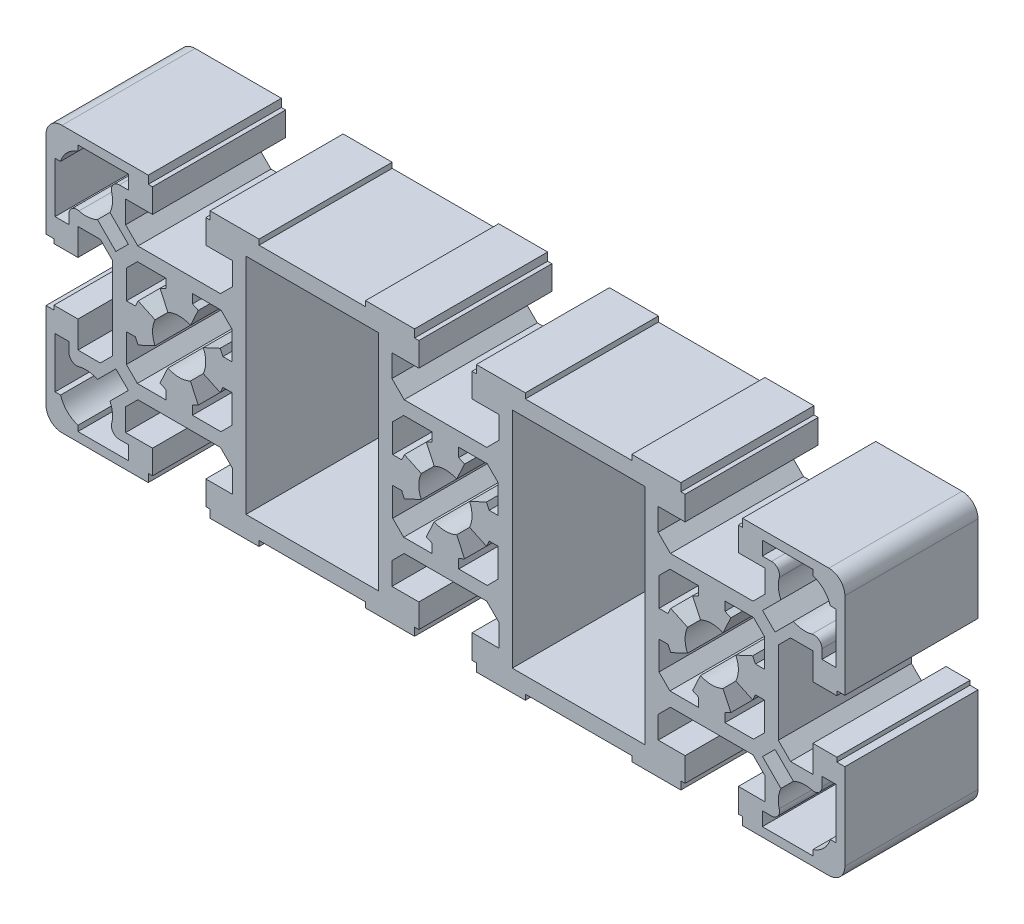
SolidWorks part; units mm, degrees
material "1060 Alloy"
ref_plane "Front" through (0, 0, 0) normal (0, 0, 1) x (1, 0, 0)
ref_plane "Top" through (0, 0, 0) normal (0, 1, 0) x (1, 0, 0)
ref_plane "Right" through (0, 0, 0) normal (1, 0, 0) x (0, 0, -1)
ref_plane "Plane1" through (0, 0, 0) normal (0, 0, 1) x (1, 0, 0)
sketch "Sketch1" plane through (0, 0, 0) normal (0, 0, 1) x (1, 0, 0)
  line L0 (72.2697, 19) -> (73.3, 19)
  line L1 (73.3, 19) -> (73.3, 9.5)
  line L2 (73.3, 9.5) -> (70.7, 9.5)
  line L3 (70.7, 9.5) -> (70.7, 11.2262)
  line L4 (65.3376, 12.9918) -> (61.8847, 9.5389)
  line L5 (61.8847, 9.5389) -> (59.5389, 11.8847)
  line L6 (59.5389, 11.8847) -> (62.9918, 15.3376)
  line L7 (61.2262, 20.7) -> (59.5, 20.7)
  line L8 (59.5, 20.7) -> (59.5, 23.3)
  line L9 (59.5, 23.3) -> (69, 23.3)
  line L10 (69, 23.3) -> (69, 22.2697)
  line L11 (62.9918, -15.3376) -> (59.5389, -11.8847)
  line L12 (59.5389, -11.8847) -> (61.8847, -9.5389)
  line L13 (61.8847, -9.5389) -> (65.3376, -12.9918)
  line L14 (70.7, -11.2262) -> (70.7, -9.5)
  line L15 (70.7, -9.5) -> (73.3, -9.5)
  line L16 (73.3, -9.5) -> (73.3, -19)
  line L17 (73.3, -19) -> (72.2697, -19)
  line L18 (69, -22.2697) -> (69, -23.3)
  line L19 (69, -23.3) -> (59.5, -23.3)
  line L20 (59.5, -23.3) -> (59.5, -20.7)
  line L21 (59.5, -20.7) -> (61.2262, -20.7)
  line L22 (-62.9918, 15.3376) -> (-59.5389, 11.8847)
  line L23 (-59.5389, 11.8847) -> (-61.8847, 9.5389)
  line L24 (-61.8847, 9.5389) -> (-65.3376, 12.9918)
  line L25 (-70.7, 11.2262) -> (-70.7, 9.5)
  line L26 (-70.7, 9.5) -> (-73.3, 9.5)
  line L27 (-73.3, 9.5) -> (-73.3, 19)
  line L28 (-73.3, 19) -> (-72.2697, 19)
  line L29 (-69, 22.2697) -> (-69, 23.3)
  line L30 (-69, 23.3) -> (-59.5, 23.3)
  line L31 (-59.5, 23.3) -> (-59.5, 20.7)
  line L32 (-59.5, 20.7) -> (-61.2262, 20.7)
  line L33 (-61.2262, -20.7) -> (-59.5, -20.7)
  line L34 (-59.5, -20.7) -> (-59.5, -23.3)
  line L35 (-59.5, -23.3) -> (-69, -23.3)
  line L36 (-69, -23.3) -> (-69, -22.2697)
  line L37 (-72.2697, -19) -> (-73.3, -19)
  line L38 (-73.3, -19) -> (-73.3, -9.5)
  line L39 (-73.3, -9.5) -> (-70.7, -9.5)
  line L40 (-70.7, -9.5) -> (-70.7, -11.2262)
  line L41 (-65.3376, -12.9918) -> (-61.8847, -9.5389)
  line L42 (-61.8847, -9.5389) -> (-59.5389, -11.8847)
  line L43 (-59.5389, -11.8847) -> (-62.9918, -15.3376)
  line L44 (-3.5923, 7.7036) -> (-2.1131, 4.5315)
  line L45 (2.1131, 4.5315) -> (3.5923, 7.7036)
  line L46 (3.5923, 7.7036) -> (2.5, 8.2129)
  line L47 (2.5, 8.2129) -> (2.5, 9.9)
  line L48 (2.5, 9.9) -> (7.8466, 9.9)
  line L49 (7.8466, 9.9) -> (9.9, 7.8466)
  line L50 (9.9, 7.8466) -> (9.9, 2.5)
  line L51 (9.9, 2.5) -> (8.2129, 2.5)
  line L52 (8.2129, 2.5) -> (7.7036, 3.5923)
  line L53 (7.7036, 3.5923) -> (4.5315, 2.1131)
  line L54 (4.5315, -2.1131) -> (7.7036, -3.5923)
  line L55 (7.7036, -3.5923) -> (8.2129, -2.5)
  line L56 (8.2129, -2.5) -> (9.9, -2.5)
  line L57 (9.9, -2.5) -> (9.9, -7.8466)
  line L58 (9.9, -7.8466) -> (7.8466, -9.9)
  line L59 (7.8466, -9.9) -> (2.5, -9.9)
  line L60 (2.5, -9.9) -> (2.5, -8.2129)
  line L61 (2.5, -8.2129) -> (3.5923, -7.7036)
  line L62 (3.5923, -7.7036) -> (2.1131, -4.5315)
  line L63 (-2.1131, -4.5315) -> (-3.5923, -7.7036)
  line L64 (-3.5923, -7.7036) -> (-2.5, -8.2129)
  line L65 (-2.5, -8.2129) -> (-2.5, -9.9)
  line L66 (-2.5, -9.9) -> (-7.8466, -9.9)
  line L67 (-7.8466, -9.9) -> (-9.9, -7.8466)
  line L68 (-9.9, -7.8466) -> (-9.9, -2.5)
  line L69 (-9.9, -2.5) -> (-8.2129, -2.5)
  line L70 (-8.2129, -2.5) -> (-7.7036, -3.5923)
  line L71 (-7.7036, -3.5923) -> (-4.5315, -2.1131)
  line L72 (-4.5315, 2.1131) -> (-7.7036, 3.5923)
  line L73 (-7.7036, 3.5923) -> (-8.2129, 2.5)
  line L74 (-8.2129, 2.5) -> (-9.9, 2.5)
  line L75 (-9.9, 2.5) -> (-9.9, 7.8466)
  line L76 (-9.9, 7.8466) -> (-7.8466, 9.9)
  line L77 (-7.8466, 9.9) -> (-2.5, 9.9)
  line L78 (-2.5, 9.9) -> (-2.5, 8.2129)
  line L79 (-2.5, 8.2129) -> (-3.5923, 7.7036)
  line L80 (52.5, 8.2129) -> (52.5, 9.9)
  line L81 (52.5, 9.9) -> (57.8466, 9.9)
  line L82 (57.8466, 9.9) -> (59.9, 7.8466)
  line L83 (59.9, 7.8466) -> (59.9, 2.5)
  line L84 (59.9, 2.5) -> (58.2129, 2.5)
  line L85 (58.2129, 2.5) -> (57.7036, 3.5923)
  line L86 (57.7036, 3.5923) -> (54.5315, 2.1131)
  line L87 (54.5315, -2.1131) -> (57.7036, -3.5923)
  line L88 (57.7036, -3.5923) -> (58.2129, -2.5)
  line L89 (58.2129, -2.5) -> (59.9, -2.5)
  line L90 (59.9, -2.5) -> (59.9, -7.8466)
  line L91 (59.9, -7.8466) -> (57.8466, -9.9)
  line L92 (57.8466, -9.9) -> (52.5, -9.9)
  line L93 (52.5, -9.9) -> (52.5, -8.2129)
  line L94 (52.5, -8.2129) -> (53.5923, -7.7036)
  line L95 (53.5923, -7.7036) -> (52.1131, -4.5315)
  line L96 (47.8869, -4.5315) -> (46.4077, -7.7036)
  line L97 (46.4077, -7.7036) -> (47.5, -8.2129)
  line L98 (47.5, -8.2129) -> (47.5, -9.9)
  line L99 (47.5, -9.9) -> (42.1534, -9.9)
  line L100 (42.1534, -9.9) -> (40.1, -7.8466)
  line L101 (40.1, -7.8466) -> (40.1, -2.5)
  line L102 (40.1, -2.5) -> (41.7871, -2.5)
  line L103 (41.7871, -2.5) -> (42.2964, -3.5923)
  line L104 (42.2964, -3.5923) -> (45.4685, -2.1131)
  line L105 (45.4685, 2.1131) -> (42.2964, 3.5923)
  line L106 (42.2964, 3.5923) -> (41.7871, 2.5)
  line L107 (41.7871, 2.5) -> (40.1, 2.5)
  line L108 (40.1, 2.5) -> (40.1, 7.8466)
  line L109 (40.1, 7.8466) -> (42.1534, 9.9)
  line L110 (42.1534, 9.9) -> (47.5, 9.9)
  line L111 (47.5, 9.9) -> (47.5, 8.2129)
  line L112 (47.5, 8.2129) -> (46.4077, 7.7036)
  line L113 (46.4077, 7.7036) -> (47.8869, 4.5315)
  line L114 (52.1131, 4.5315) -> (53.5923, 7.7036)
  line L115 (53.5923, 7.7036) -> (52.5, 8.2129)
  line L116 (-40.1, 2.5) -> (-41.7871, 2.5)
  line L117 (-41.7871, 2.5) -> (-42.2964, 3.5923)
  line L118 (-42.2964, 3.5923) -> (-45.4685, 2.1131)
  line L119 (-45.4685, -2.1131) -> (-42.2964, -3.5923)
  line L120 (-42.2964, -3.5923) -> (-41.7871, -2.5)
  line L121 (-41.7871, -2.5) -> (-40.1, -2.5)
  line L122 (-40.1, -2.5) -> (-40.1, -7.8466)
  line L123 (-40.1, -7.8466) -> (-42.1534, -9.9)
  line L124 (-42.1534, -9.9) -> (-47.5, -9.9)
  line L125 (-47.5, -9.9) -> (-47.5, -8.2129)
  line L126 (-47.5, -8.2129) -> (-46.4077, -7.7036)
  line L127 (-46.4077, -7.7036) -> (-47.8869, -4.5315)
  line L128 (-52.1131, -4.5315) -> (-53.5923, -7.7036)
  line L129 (-53.5923, -7.7036) -> (-52.5, -8.2129)
  line L130 (-52.5, -8.2129) -> (-52.5, -9.9)
  line L131 (-52.5, -9.9) -> (-57.8466, -9.9)
  line L132 (-57.8466, -9.9) -> (-59.9, -7.8466)
  line L133 (-59.9, -7.8466) -> (-59.9, -2.5)
  line L134 (-59.9, -2.5) -> (-58.2129, -2.5)
  line L135 (-58.2129, -2.5) -> (-57.7036, -3.5923)
  line L136 (-57.7036, -3.5923) -> (-54.5315, -2.1131)
  line L137 (-54.5315, 2.1131) -> (-57.7036, 3.5923)
  line L138 (-57.7036, 3.5923) -> (-58.2129, 2.5)
  line L139 (-58.2129, 2.5) -> (-59.9, 2.5)
  line L140 (-59.9, 2.5) -> (-59.9, 7.8466)
  line L141 (-59.9, 7.8466) -> (-57.8466, 9.9)
  line L142 (-57.8466, 9.9) -> (-52.5, 9.9)
  line L143 (-52.5, 9.9) -> (-52.5, 8.2129)
  line L144 (-52.5, 8.2129) -> (-53.5923, 7.7036)
  line L145 (-53.5923, 7.7036) -> (-52.1131, 4.5315)
  line L146 (-47.8869, 4.5315) -> (-46.4077, 7.7036)
  line L147 (-46.4077, 7.7036) -> (-47.5, 8.2129)
  line L148 (-47.5, 8.2129) -> (-47.5, 9.9)
  line L149 (-47.5, 9.9) -> (-42.1534, 9.9)
  line L150 (-42.1534, 9.9) -> (-40.1, 7.8466)
  line L151 (-40.1, 7.8466) -> (-40.1, 2.5)
  line L152 (-37.45, -21) -> (-37.45, 21)
  line L153 (-37.45, 21) -> (-12.55, 21)
  line L154 (-12.55, 21) -> (-12.55, -21)
  line L155 (-12.55, -21) -> (-37.45, -21)
  line L156 (12.55, 21) -> (37.45, 21)
  line L157 (37.45, 21) -> (37.45, -21)
  line L158 (37.45, -21) -> (12.55, -21)
  line L159 (12.55, -21) -> (12.55, 21)
  line L160 (73.5, 5) -> (73.5, 5.8)
  line L161 (73.5, 5.8) -> (75, 5.8)
  line L162 (75, 5.8) -> (75, 22)
  line L163 (72, 25) -> (55.8, 25)
  line L164 (55.8, 25) -> (55.8, 23.5)
  line L165 (55.8, 23.5) -> (55, 23.5)
  line L166 (55, 23.5) -> (55, 19)
  line L167 (55, 19) -> (60.05, 19)
  line L168 (60.05, 19) -> (60.05, 14.8)
  line L169 (60.05, 14.8) -> (57.75, 12.5)
  line L170 (57.75, 12.5) -> (42.25, 12.5)
  line L171 (42.25, 12.5) -> (39.95, 14.8)
  line L172 (39.95, 14.8) -> (39.95, 19)
  line L173 (39.95, 19) -> (45, 19)
  line L174 (45, 19) -> (45, 23.5)
  line L175 (45, 23.5) -> (44.2, 23.5)
  line L176 (44.2, 23.5) -> (44.2, 25)
  line L177 (44.2, 25) -> (35, 25)
  line L178 (35, 25) -> (35, 24)
  line L179 (35, 24) -> (15, 24)
  line L180 (15, 24) -> (15, 25)
  line L181 (15, 25) -> (5.8, 25)
  line L182 (5.8, 25) -> (5.8, 23.5)
  line L183 (5.8, 23.5) -> (5, 23.5)
  line L184 (5, 23.5) -> (5, 19)
  line L185 (5, 19) -> (10.05, 19)
  line L186 (10.05, 19) -> (10.05, 14.8)
  line L187 (10.05, 14.8) -> (7.75, 12.5)
  line L188 (7.75, 12.5) -> (-7.75, 12.5)
  line L189 (-7.75, 12.5) -> (-10.05, 14.8)
  line L190 (-10.05, 14.8) -> (-10.05, 19)
  line L191 (-10.05, 19) -> (-5, 19)
  line L192 (-5, 19) -> (-5, 23.5)
  line L193 (-5, 23.5) -> (-5.8, 23.5)
  line L194 (-5.8, 23.5) -> (-5.8, 25)
  line L195 (-5.8, 25) -> (-15, 25)
  line L196 (-15, 25) -> (-15, 24)
  line L197 (-15, 24) -> (-35, 24)
  line L198 (-35, 24) -> (-35, 25)
  line L199 (-35, 25) -> (-44.2, 25)
  line L200 (-44.2, 25) -> (-44.2, 23.5)
  line L201 (-44.2, 23.5) -> (-45, 23.5)
  line L202 (-45, 23.5) -> (-45, 19)
  line L203 (-45, 19) -> (-39.95, 19)
  line L204 (-39.95, 19) -> (-39.95, 14.8)
  line L205 (-39.95, 14.8) -> (-42.25, 12.5)
  line L206 (-42.25, 12.5) -> (-57.75, 12.5)
  line L207 (-57.75, 12.5) -> (-60.05, 14.8)
  line L208 (-60.05, 14.8) -> (-60.05, 19)
  line L209 (-60.05, 19) -> (-55, 19)
  line L210 (-55, 19) -> (-55, 23.5)
  line L211 (-55, 23.5) -> (-55.8, 23.5)
  line L212 (-55.8, 23.5) -> (-55.8, 25)
  line L213 (-55.8, 25) -> (-72, 25)
  line L214 (-75, 22) -> (-75, 5.8)
  line L215 (-75, 5.8) -> (-73.5, 5.8)
  line L216 (-73.5, 5.8) -> (-73.5, 5)
  line L217 (-73.5, 5) -> (-69, 5)
  line L218 (-69, 5) -> (-69, 10.05)
  line L219 (-69, 10.05) -> (-64.8, 10.05)
  line L220 (-64.8, 10.05) -> (-62.5, 7.75)
  line L221 (-62.5, 7.75) -> (-62.5, -7.75)
  line L222 (-62.5, -7.75) -> (-64.8, -10.05)
  line L223 (-64.8, -10.05) -> (-69, -10.05)
  line L224 (-69, -10.05) -> (-69, -5)
  line L225 (-69, -5) -> (-73.5, -5)
  line L226 (-73.5, -5) -> (-73.5, -5.8)
  line L227 (-73.5, -5.8) -> (-75, -5.8)
  line L228 (-75, -5.8) -> (-75, -22)
  line L229 (-72, -25) -> (-55.8, -25)
  line L230 (-55.8, -25) -> (-55.8, -23.5)
  line L231 (-55.8, -23.5) -> (-55, -23.5)
  line L232 (-55, -23.5) -> (-55, -19)
  line L233 (-55, -19) -> (-60.05, -19)
  line L234 (-60.05, -19) -> (-60.05, -14.8)
  line L235 (-60.05, -14.8) -> (-57.75, -12.5)
  line L236 (-57.75, -12.5) -> (-42.25, -12.5)
  line L237 (-42.25, -12.5) -> (-39.95, -14.8)
  line L238 (-39.95, -14.8) -> (-39.95, -19)
  line L239 (-39.95, -19) -> (-45, -19)
  line L240 (-45, -19) -> (-45, -23.5)
  line L241 (-45, -23.5) -> (-44.2, -23.5)
  line L242 (-44.2, -23.5) -> (-44.2, -25)
  line L243 (-44.2, -25) -> (-35, -25)
  line L244 (-35, -25) -> (-35, -24)
  line L245 (-35, -24) -> (-15, -24)
  line L246 (-15, -24) -> (-15, -25)
  line L247 (-15, -25) -> (-5.8, -25)
  line L248 (-5.8, -25) -> (-5.8, -23.5)
  line L249 (-5.8, -23.5) -> (-5, -23.5)
  line L250 (-5, -23.5) -> (-5, -19)
  line L251 (-5, -19) -> (-10.05, -19)
  line L252 (-10.05, -19) -> (-10.05, -14.8)
  line L253 (-10.05, -14.8) -> (-7.75, -12.5)
  line L254 (-7.75, -12.5) -> (7.75, -12.5)
  line L255 (7.75, -12.5) -> (10.05, -14.8)
  line L256 (10.05, -14.8) -> (10.05, -19)
  line L257 (10.05, -19) -> (5, -19)
  line L258 (5, -19) -> (5, -23.5)
  line L259 (5, -23.5) -> (5.8, -23.5)
  line L260 (5.8, -23.5) -> (5.8, -25)
  line L261 (5.8, -25) -> (15, -25)
  line L262 (15, -25) -> (15, -24)
  line L263 (15, -24) -> (35, -24)
  line L264 (35, -24) -> (35, -25)
  line L265 (35, -25) -> (44.2, -25)
  line L266 (44.2, -25) -> (44.2, -23.5)
  line L267 (44.2, -23.5) -> (45, -23.5)
  line L268 (45, -23.5) -> (45, -19)
  line L269 (45, -19) -> (39.95, -19)
  line L270 (39.95, -19) -> (39.95, -14.8)
  line L271 (39.95, -14.8) -> (42.25, -12.5)
  line L272 (42.25, -12.5) -> (57.75, -12.5)
  line L273 (57.75, -12.5) -> (60.05, -14.8)
  line L274 (60.05, -14.8) -> (60.05, -19)
  line L275 (60.05, -19) -> (55, -19)
  line L276 (55, -19) -> (55, -23.5)
  line L277 (55, -23.5) -> (55.8, -23.5)
  line L278 (55.8, -23.5) -> (55.8, -25)
  line L279 (55.8, -25) -> (72, -25)
  line L280 (75, -22) -> (75, -5.8)
  line L281 (75, -5.8) -> (73.5, -5.8)
  line L282 (73.5, -5.8) -> (73.5, -5)
  line L283 (73.5, -5) -> (69, -5)
  line L284 (69, -5) -> (69, -10.05)
  line L285 (69, -10.05) -> (64.8, -10.05)
  line L286 (64.8, -10.05) -> (62.5, -7.75)
  line L287 (62.5, -7.75) -> (62.5, 7.75)
  line L288 (62.5, 7.75) -> (64.8, 10.05)
  line L289 (64.8, 10.05) -> (69, 10.05)
  line L290 (69, 10.05) -> (69, 5)
  line L291 (69, 5) -> (73.5, 5)
  arc A0 (69, 22.2697) -> (72.2697, 19) centre (67.5, 17.5) cw
  arc A1 (70.7, 11.2262) -> (68.8077, 12.674) centre (69.2, 11.2262) ccw
  arc A2 (68.8077, 12.674) -> (65.3376, 12.9918) centre (67.5, 17.5) cw
  arc A3 (62.9918, 15.3376) -> (62.674, 18.8077) centre (67.5, 17.5) cw
  arc A4 (62.674, 18.8077) -> (61.2262, 20.7) centre (61.2262, 19.2) ccw
  arc A5 (65.3376, -12.9918) -> (68.8077, -12.674) centre (67.5, -17.5) cw
  arc A6 (68.8077, -12.674) -> (70.7, -11.2262) centre (69.2, -11.2262) ccw
  arc A7 (72.2697, -19) -> (69, -22.2697) centre (67.5, -17.5) cw
  arc A8 (61.2262, -20.7) -> (62.674, -18.8077) centre (61.2262, -19.2) ccw
  arc A9 (62.674, -18.8077) -> (62.9918, -15.3376) centre (67.5, -17.5) cw
  arc A10 (-61.2262, 20.7) -> (-62.674, 18.8077) centre (-61.2262, 19.2) ccw
  arc A11 (-62.674, 18.8077) -> (-62.9918, 15.3376) centre (-67.5, 17.5) cw
  arc A12 (-65.3376, 12.9918) -> (-68.8077, 12.674) centre (-67.5, 17.5) cw
  arc A13 (-68.8077, 12.674) -> (-70.7, 11.2262) centre (-69.2, 11.2262) ccw
  arc A14 (-72.2697, 19) -> (-69, 22.2697) centre (-67.5, 17.5) cw
  arc A15 (-62.9918, -15.3376) -> (-62.674, -18.8077) centre (-67.5, -17.5) cw
  arc A16 (-62.674, -18.8077) -> (-61.2262, -20.7) centre (-61.2262, -19.2) ccw
  arc A17 (-69, -22.2697) -> (-72.2697, -19) centre (-67.5, -17.5) cw
  arc A18 (-70.7, -11.2262) -> (-68.8077, -12.674) centre (-69.2, -11.2262) ccw
  arc A19 (-68.8077, -12.674) -> (-65.3376, -12.9918) centre (-67.5, -17.5) cw
  arc A20 (-2.1131, 4.5315) -> (2.1131, 4.5315) centre (0, 0) cw
  arc A21 (4.5315, 2.1131) -> (4.5315, -2.1131) centre (0, 0) cw
  arc A22 (2.1131, -4.5315) -> (-2.1131, -4.5315) centre (0, 0) cw
  arc A23 (-4.5315, -2.1131) -> (-4.5315, 2.1131) centre (0, 0) cw
  arc A24 (54.5315, 2.1131) -> (54.5315, -2.1131) centre (50, 0) cw
  arc A25 (52.1131, -4.5315) -> (47.8869, -4.5315) centre (50, 0) cw
  arc A26 (45.4685, -2.1131) -> (45.4685, 2.1131) centre (50, 0) cw
  arc A27 (47.8869, 4.5315) -> (52.1131, 4.5315) centre (50, 0) cw
  arc A28 (-45.4685, 2.1131) -> (-45.4685, -2.1131) centre (-50, 0) cw
  arc A29 (-47.8869, -4.5315) -> (-52.1131, -4.5315) centre (-50, 0) cw
  arc A30 (-54.5315, -2.1131) -> (-54.5315, 2.1131) centre (-50, 0) cw
  arc A31 (-52.1131, 4.5315) -> (-47.8869, 4.5315) centre (-50, 0) cw
  arc A32 (75, 22) -> (72, 25) centre (72, 22) ccw
  arc A33 (-72, 25) -> (-75, 22) centre (-72, 22) ccw
  arc A34 (-75, -22) -> (-72, -25) centre (-72, -22) ccw
  arc A35 (72, -25) -> (75, -22) centre (72, -22) ccw
extrude "Boss-Extrude1" add sketch "Sketch1" against normal blind 25
